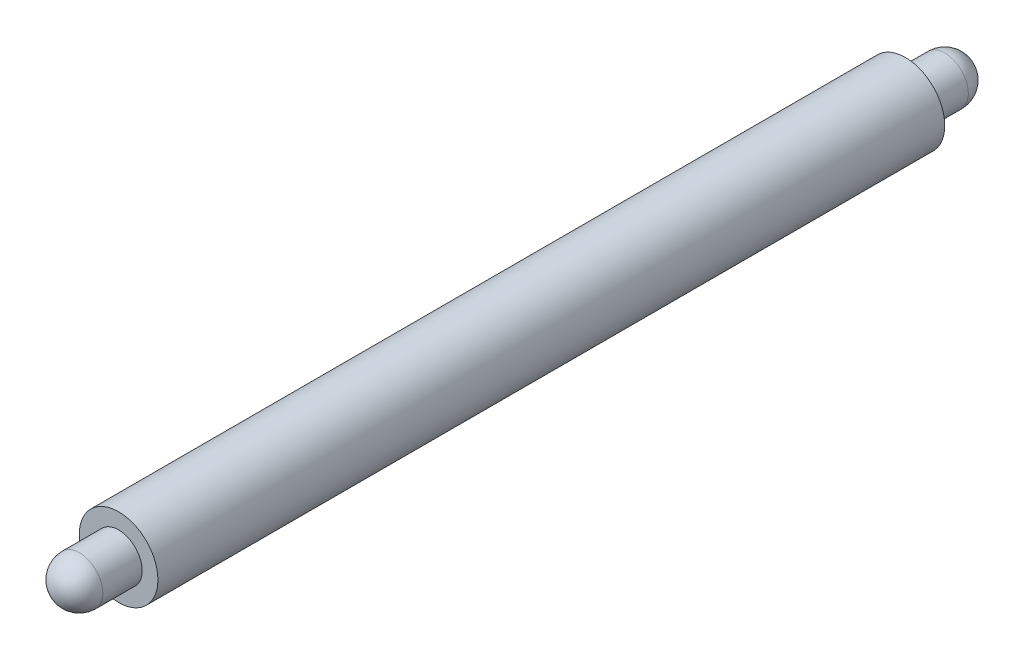
SolidWorks part; units mm, degrees
material "C-Glass Fiber"
ref_plane "Front Plane" through (0, 0, 0) normal (0, 0, 1) x (1, 0, 0)
ref_plane "Top Plane" through (0, 0, 0) normal (0, 1, 0) x (1, 0, 0)
ref_plane "Right Plane" through (0, 0, 0) normal (1, 0, 0) x (0, 0, -1)
sketch "Sketch1" plane through (0, 0, 0) normal (0, 0, 1) x (1, 0, 0)
  circle A0 centre (-48.1041, 10.2306) radius 5
extrude "Boss-Extrude1" add sketch "Sketch1" along normal blind 100
sketch "Sketch2" plane through (0, 0, 100) normal (0, 0, 1) x (1, 0, 0)
  circle A0 centre (-48.1041, 10.2306) radius 3
extrude "Boss-Extrude2" add sketch "Sketch2" along normal blind 8
sketch "Sketch4" plane through (0, 0, 0) normal (0, 0, -1) x (-1, 0, 0)
  circle A0 centre (48.1041, 10.2306) radius 3
extrude "Boss-Extrude3" add sketch "Sketch4" along normal blind 8
fillet "Fillet1" radius 3 2 edges at (-45.1041, 10.2306, 108) (-51.1041, 10.2306, -8)
